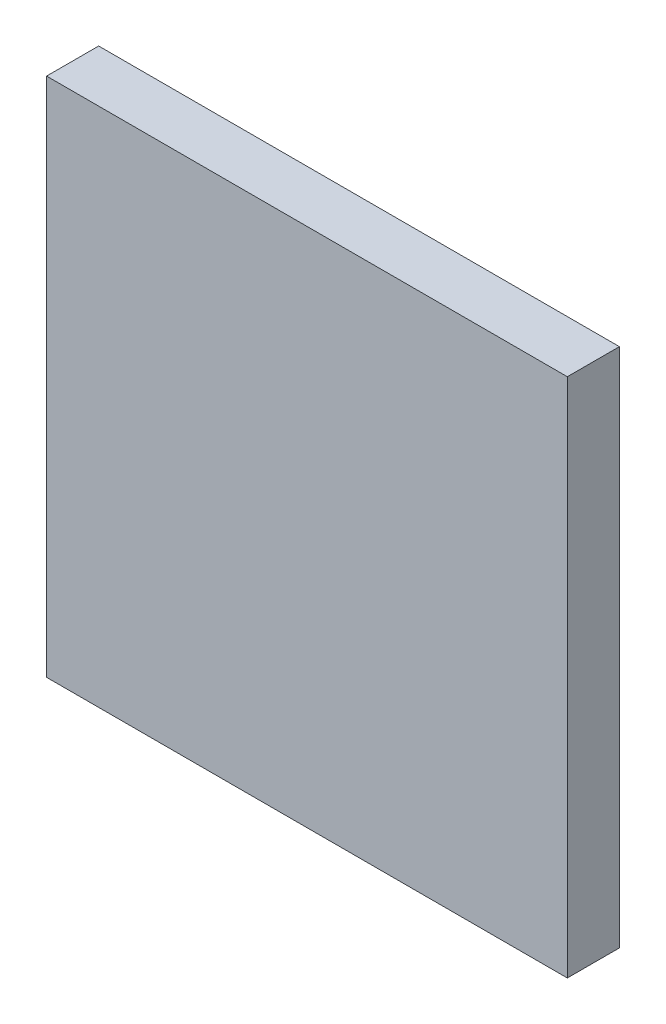
SolidWorks part; units mm, degrees
ref_plane "Plano frontal" through (0, 0, 0) normal (0, 0, 1) x (1, 0, 0)
ref_plane "Plano superior" through (0, 0, 0) normal (0, 1, 0) x (1, 0, 0)
ref_plane "Plano direito" through (0, 0, 0) normal (1, 0, 0) x (0, 0, -1)
sketch "Esboço1" plane through (0, 0, 0) normal (0, 0, 1) x (1, 0, 0)
  line L0 (0, 0) -> (0, 10)
  line L1 (0, 10) -> (10, 10)
  line L2 (10, 10) -> (10, 0)
  line L3 (10, 0) -> (0, 0)
extrude "Ressalto-extrusão1" add sketch "Esboço1" along normal blind 1
